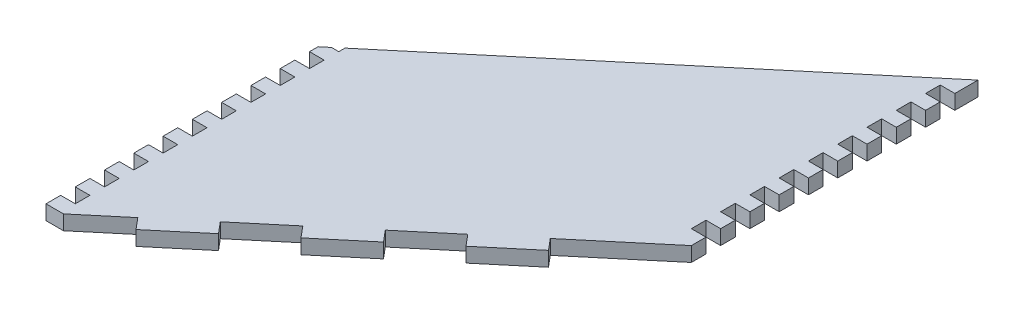
SolidWorks part; units mm, degrees
ref_plane "Front Plane" through (0, 0, 0) normal (0, 0, 1) x (1, 0, 0)
ref_plane "Top Plane" through (0, 0, 0) normal (0, 1, 0) x (1, 0, 0)
ref_plane "Right Plane" through (0, 0, 0) normal (1, 0, 0) x (0, 0, -1)
sketch "Sketch1" plane through (0, 0, 0) normal (0, 1, 0) x (1, 0, 0)
  line L0 (-45.4921, -38.0131) -> (-45.4921, 94.6163)
  line L1 (-45.4921, -38.0131) -> (110.1681, 92.6014)
  line L2 (110.1681, 92.6014) -> (110.1681, 225.2308)
  line L3 (-45.4921, 94.6163) -> (110.1681, 225.2308)
  dimension "D1" = 50
  dimension "D2" = 101.6
  dimension "D3" = 203.2
extrude "Boss-Extrude1" add sketch "Sketch1" along normal blind 6.35
sketch "Sketch2" plane through (0, 6.35, 0) normal (0, 1, 0) x (1, 0, 0)
  line L0 (-45.4921, -38.0131) -> (110.1681, 92.6014) construction
  line L1 (-45.4921, -38.0131) -> (-16.3058, -13.5229)
  line L2 (-45.4921, -38.0131) -> (-49.5738, -33.1487)
  line L3 (-49.5738, -33.1487) -> (-20.3875, -8.6585)
  line L4 (-16.3058, -13.5229) -> (-20.3875, -8.6585)
  line L6 (-0.93, 7.6683) -> (3.1517, 2.8039)
  line L7 (-0.93, 7.6683) -> (18.5276, 23.9951)
  line L8 (18.5276, 23.9951) -> (22.6093, 19.1307)
  line L9 (3.1517, 2.8039) -> (22.6093, 19.1307)
  line L10 (37.9851, 40.3219) -> (42.0668, 35.4576)
  line L11 (37.9851, 40.3219) -> (57.4426, 56.6487)
  line L12 (57.4426, 56.6487) -> (61.5243, 51.7844)
  line L13 (42.0668, 35.4576) -> (61.5243, 51.7844)
  line L14 (80.9818, 68.1112) -> (115.0325, 96.6831)
  line L15 (80.9818, 68.1112) -> (76.9001, 72.9755)
  line L16 (76.9001, 72.9755) -> (110.9508, 101.5475)
  line L17 (115.0325, 96.6831) -> (110.9508, 101.5475)
  point P19 (78.941, 70.5434)
  dimension "D1" = 6.35
  dimension "D2" = 38.1
  dimension "D3" = 6.35
  dimension "D4" = 25.4
  dimension "D5" = 25.4
  dimension "D6" = 6.35
  dimension "D7" = 25.4
  dimension "D8" = 25.4
  dimension "D9" = 6.35
  dimension "D10" = 44.45
  dimension "D11" = 25.4
extrude "Cut-Extrude1" cut sketch "Sketch2" against normal through all
sketch "Sketch3" plane through (0, 6.35, 0) normal (0, 1, 0) x (1, 0, 0)
  line L0 (110.1681, 100.8907) -> (110.1681, 225.2308) construction
  line L1 (103.8181, 113.5907) -> (110.1681, 113.5907)
  line L2 (103.8181, 113.5907) -> (103.8181, 107.2407)
  line L3 (103.8181, 107.2407) -> (110.1681, 107.2407)
  line L4 (110.1681, 113.5907) -> (110.1681, 107.2407)
  line L5 (103.8181, 126.2907) -> (110.1681, 126.2907)
  line L6 (103.8181, 126.2907) -> (103.8181, 119.9407)
  line L7 (103.8181, 119.9407) -> (110.1681, 119.9407)
  line L8 (110.1681, 126.2907) -> (110.1681, 119.9407)
  line L9 (-3.175, 3.2811) -> (3.175, 3.2811)
  line L10 (-3.175, 3.2811) -> (-3.175, -3.175)
  line L11 (-3.175, -3.175) -> (3.175, -3.175)
  line L12 (3.175, 3.2811) -> (3.175, -3.175)
  line L13 (103.8181, 138.9907) -> (110.1681, 138.9907)
  line L14 (103.8181, 138.9907) -> (103.8181, 132.6407)
  line L15 (103.8181, 132.6407) -> (110.1681, 132.6407)
  line L16 (110.1681, 138.9907) -> (110.1681, 132.6407)
  line L17 (-3.175, 3.2811) -> (3.175, 3.2811)
  line L18 (-3.175, 3.2811) -> (-3.175, -3.175)
  line L19 (-3.175, -3.175) -> (3.175, -3.175)
  line L20 (3.175, 3.2811) -> (3.175, -3.175)
  line L21 (103.8181, 151.6907) -> (110.1681, 151.6907)
  line L22 (103.8181, 151.6907) -> (103.8181, 145.3407)
  line L23 (103.8181, 145.3407) -> (110.1681, 145.3407)
  line L24 (110.1681, 151.6907) -> (110.1681, 145.3407)
  line L25 (-3.175, 3.175) -> (3.175, 3.175)
  line L26 (-3.175, 3.175) -> (-3.175, -3.175)
  line L27 (-3.175, -3.175) -> (3.175, -3.175)
  line L28 (3.175, 3.175) -> (3.175, -3.175)
  line L29 (103.8181, 164.3907) -> (110.1681, 164.3907)
  line L30 (103.8181, 164.3907) -> (103.8181, 158.0407)
  line L31 (103.8181, 158.0407) -> (110.1681, 158.0407)
  line L32 (110.1681, 164.3907) -> (110.1681, 158.0407)
  line L33 (-3.175, 3.175) -> (3.175, 3.175)
  line L34 (-3.175, 3.175) -> (-3.175, -3.175)
  line L35 (-3.175, -3.175) -> (3.175, -3.175)
  line L36 (3.175, 3.175) -> (3.175, -3.175)
  line L37 (103.8181, 177.0907) -> (110.1681, 177.0907)
  line L38 (103.8181, 177.0907) -> (103.8181, 170.7407)
  line L39 (103.8181, 170.7407) -> (110.1681, 170.7407)
  line L40 (110.1681, 177.0907) -> (110.1681, 170.7407)
  line L41 (103.8181, 189.7907) -> (110.1681, 189.7907)
  line L42 (103.8181, 189.7907) -> (103.8181, 183.4407)
  line L43 (103.8181, 183.4407) -> (110.1681, 183.4407)
  line L44 (110.1681, 189.7907) -> (110.1681, 183.4407)
  line L45 (103.8181, 202.4907) -> (110.1681, 202.4907)
  line L46 (103.8181, 202.4907) -> (103.8181, 196.1407)
  line L47 (103.8181, 196.1407) -> (110.1681, 196.1407)
  line L48 (110.1681, 202.4907) -> (110.1681, 196.1407)
  line L49 (103.8181, 215.1907) -> (110.1681, 215.1907)
  line L50 (103.8181, 215.1907) -> (103.8181, 208.8407)
  line L51 (103.8181, 208.8407) -> (110.1681, 208.8407)
  line L52 (110.1681, 215.1907) -> (110.1681, 208.8407)
  point P4 (93.0618, 101.4552)
  line M49 (110.1681, 100.8907) -> (110.1681, 225.2308)
  dimension "D1" = 6.35
  dimension "D2" = 6.35
  dimension "D3" = 6.35
  dimension "D4" = 6.35
  dimension "D5" = 6.35
  dimension "D6" = 6.35
  dimension "D7" = 6.35
  dimension "D8" = 6.35
  dimension "D9" = 6.35
  dimension "D10" = 6.35
  dimension "D11" = 6.35
extrude "Cut-Extrude2" cut sketch "Sketch3" against normal through all contours L14 L15 L13 M49 | L6 L7 L5 M49 | L2 L3 L1 M49 | L22 L23 L21 M49 | L38 L39 L37 M49 | L42 L43 L41 M49 | L50 L51 L49 M49 | L30 L31 L32 L29 | L47 L48 L45 L46
sketch "Sketch4" plane through (0, 6.35, 0) normal (0, 1, 0) x (1, 0, 0)
  line L0 (-45.4921, 94.6163) -> (-45.4921, -29.7237) construction
  line L1 (-32.7921, -23.3737) -> (-45.4921, -23.3737)
  line L2 (-32.7921, -23.3737) -> (-32.7921, -29.7237)
  line L3 (-32.7921, -29.7237) -> (-45.4921, -29.7237)
  line L4 (-45.4921, -23.3737) -> (-45.4921, -29.7237)
  line L5 (-45.4921, -4.3237) -> (-39.1421, -4.3237)
  line L6 (-45.4921, -17.0237) -> (-39.1421, -17.0237)
  line L7 (-45.4921, -17.0237) -> (-45.4921, -10.6737)
  line L8 (-45.4921, -10.6737) -> (-39.1421, -10.6737)
  line L9 (-39.1421, -17.0237) -> (-39.1421, -10.6737)
  line L10 (-45.4921, -4.3237) -> (-45.4921, 2.0263)
  line L11 (-45.4921, 2.0263) -> (-39.1421, 2.0263)
  line L12 (-39.1421, -4.3237) -> (-39.1421, 2.0263)
  line L13 (-45.4921, 8.3763) -> (-39.1421, 8.3763)
  line L14 (-45.4921, 8.3763) -> (-45.4921, 14.7263)
  line L15 (-45.4921, 14.7263) -> (-39.1421, 14.7263)
  line L16 (-39.1421, 8.3763) -> (-39.1421, 14.7263)
  line L17 (-45.4921, 21.0763) -> (-39.1421, 21.0763)
  line L18 (-45.4921, 21.0763) -> (-45.4921, 27.4263)
  line L19 (-45.4921, 27.4263) -> (-39.1421, 27.4263)
  line L20 (-39.1421, 21.0763) -> (-39.1421, 27.4263)
  line L25 (-45.4921, 33.7763) -> (-39.1421, 33.7763)
  line L26 (-45.4921, 33.7763) -> (-45.4921, 40.1263)
  line L27 (-45.4921, 40.1263) -> (-39.1421, 40.1263)
  line L28 (-39.1421, 33.7763) -> (-39.1421, 40.1263)
  line L29 (-45.4921, 46.4763) -> (-39.1421, 46.4763)
  line L30 (-45.4921, 46.4763) -> (-45.4921, 52.8263)
  line L31 (-45.4921, 52.8263) -> (-39.1421, 52.8263)
  line L32 (-39.1421, 46.4763) -> (-39.1421, 52.8263)
  line L33 (-45.4921, 59.1763) -> (-39.1421, 59.1763)
  line L34 (-45.4921, 59.1763) -> (-45.4921, 65.5263)
  line L35 (-45.4921, 65.5263) -> (-39.1421, 65.5263)
  line L36 (-39.1421, 59.1763) -> (-39.1421, 65.5263)
  line L37 (-45.4921, 71.8763) -> (-39.1421, 71.8763)
  line L38 (-45.4921, 71.8763) -> (-45.4921, 78.2263)
  line L39 (-45.4921, 78.2263) -> (-39.1421, 78.2263)
  line L40 (-39.1421, 71.8763) -> (-39.1421, 78.2263)
  line L41 (-45.4921, 84.5763) -> (-39.1421, 84.5763)
  line L42 (-45.4921, 84.5763) -> (-45.4921, 90.9263)
  line L43 (-45.4921, 90.9263) -> (-39.1421, 90.9263)
  line L44 (-39.1421, 84.5763) -> (-39.1421, 90.9263)
  line L45 (-45.4921, 97.2763) -> (-39.1421, 97.2763)
  line L46 (-45.4921, 97.2763) -> (-45.4921, 103.6263)
  line L47 (-45.4921, 103.6263) -> (-39.1421, 103.6263)
  line L48 (-39.1421, 97.2763) -> (-39.1421, 103.6263)
  point P6 (-45.4921, -26.5487)
  dimension "D1" = 6.35
  dimension "D2" = 12.7
  dimension "D3" = 6.35
  dimension "D4" = 6.35
  dimension "D5" = 6.35
  dimension "D6" = 6.35
  dimension "D7" = 6.35
  dimension "D8" = 6.35
  dimension "D9" = 6.35
  dimension "D10" = 6.35
  dimension "D11" = 6.35
  dimension "D12" = 6.35
  dimension "D13" = 6.35
  dimension "D14" = 6.35
  dimension "D15" = 6.35
  dimension "D16" = 6.35
  dimension "D17" = 6.35
  dimension "D18" = 6.35
  dimension "D19" = 6.35
  dimension "D20" = 6.35
  dimension "D21" = 6.35
  dimension "D22" = 6.35
  dimension "D23" = 6.35
  dimension "D24" = 6.35
  dimension "D25" = 6.35
  dimension "D26" = 6.35
  dimension "D27" = 6.35
extrude "Cut-Extrude3" cut sketch "Sketch4" against normal through all
